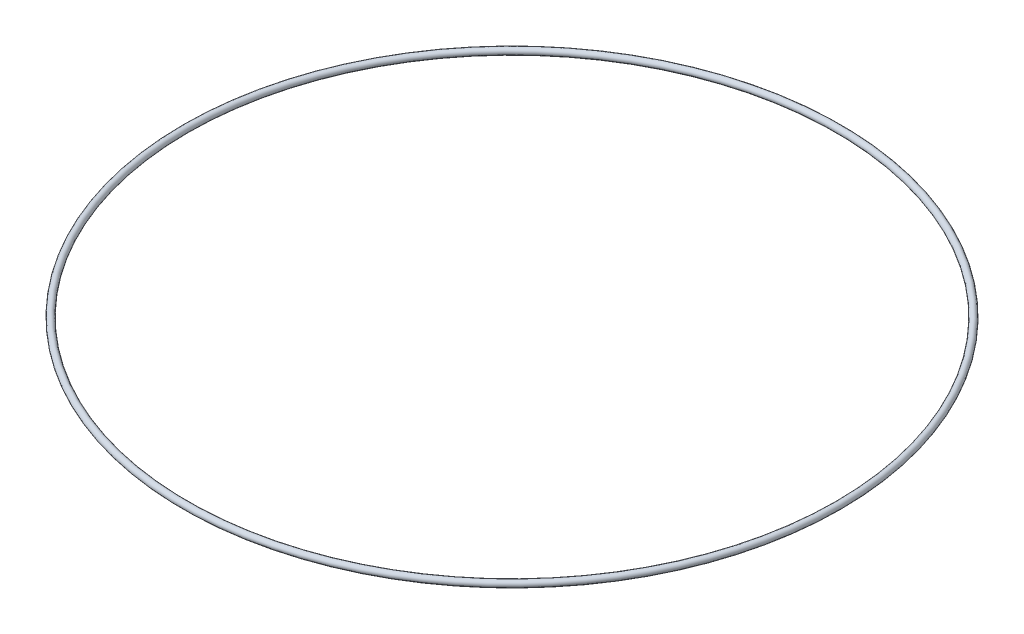
SolidWorks part; units mm, degrees
ref_plane "Front Plane" through (0, 0, 0) normal (0, 0, 1) x (1, 0, 0)
ref_plane "Top Plane" through (0, 0, 0) normal (0, 1, 0) x (1, 0, 0)
ref_plane "Right Plane" through (0, 0, 0) normal (1, 0, 0) x (0, 0, -1)
sketch "Sketch1" plane through (0, 0, 0) normal (0, 1, 0) x (1, 0, 0)
  circle A0 centre (0, 0) radius 5
  dimension "D1" = 10
sketch "Sketch3" plane through (0, 0, 0) normal (0, 1, 0) x (1, 0, 0)
  line L0 (0, -1000) -> (0, 49000) construction
  line L2 (-1000, 0) -> (49000, 0) construction
sketch "Sketch2" plane through (0, 0, 0) normal (0, 1, 0) x (1, 0, 0)
  line L0 (0, 0) -> (3.2139, 3.8302)
  line L1 (0, 0) -> (3.2139, -3.8302)
  line L2 (0, -201000) -> (0, 249000) construction
  circle A0 centre (0, 0) radius 5 construction
  dimension "D1" = 100
  dimension "D2" = 40
sketch "Sketch4" plane through (0, 0, 0) normal (0, 1, 0) x (1, 0, 0)
  line L0 (3.2139, 3.8302) -> (3.2139, -3.8302)
sketch "Sketch5" plane through (0, 0, 0) normal (0, 0, 1) x (1, 0, 0)
  line L0 (-201000, 0) -> (249000, 0) construction
  circle A0 centre (-5, 0) radius 0.05
  dimension "D2" = 0.1
  dimension "D1" = 5
sweep "Sweep1" add profiles "Sketch5" path "Sketch1"
